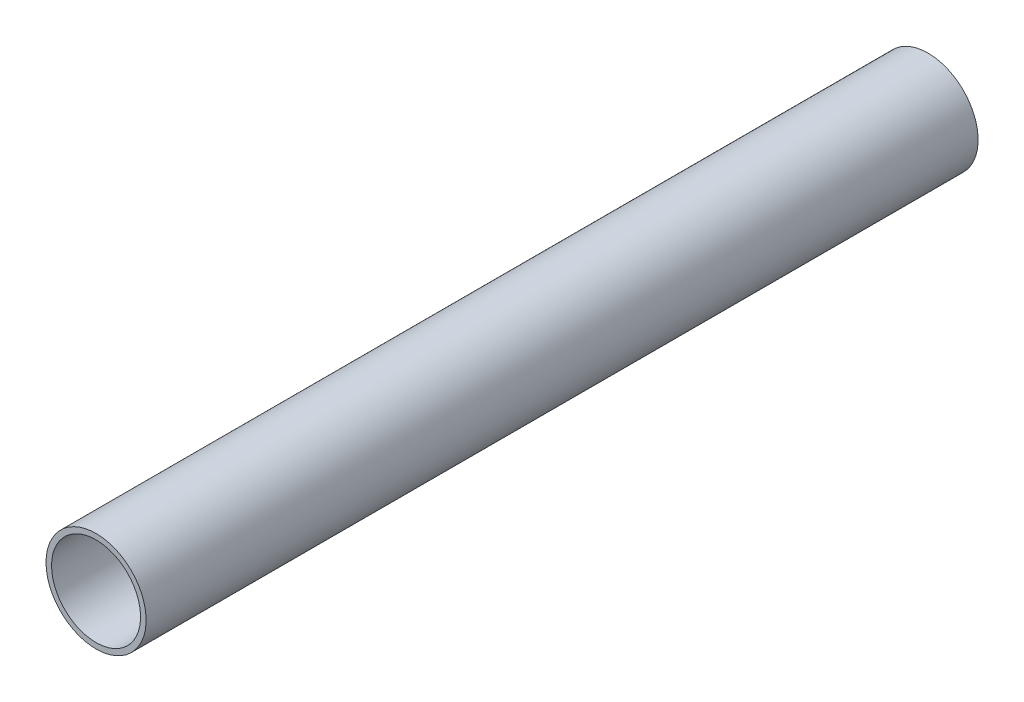
SolidWorks part; units mm, degrees
ref_plane "前视基准面" through (0, 0, 0) normal (0, 0, 1) x (1, 0, 0)
ref_plane "上视基准面" through (0, 0, 0) normal (0, 1, 0) x (1, 0, 0)
ref_plane "右视基准面" through (0, 0, 0) normal (1, 0, 0) x (0, 0, -1)
ref_plane "基准面4" through (0, 0, 0) normal (0, -1, 0) x (1, 0, 0)
sketch "草图1" plane through (0, 0, 0) normal (0, -1, 0) x (1, 0, 0)
  line L0 (50.8, -475) -> (57.15, -475)
  line L1 (57.15, -475) -> (57.15, 475)
  line L2 (57.15, 475) -> (50.8, 475)
  line L3 (50.8, 475) -> (50.8, -475)
  line L4 (0, 475) -> (0, -475) construction
revolve "旋转1" add sketch "草图1" angle 360 about L4
